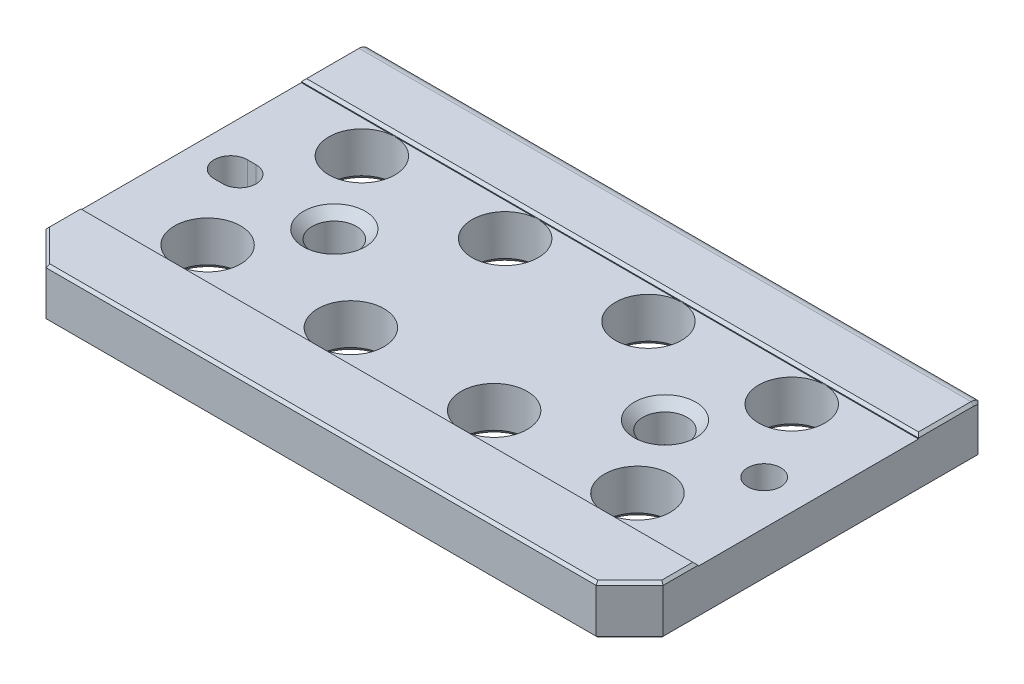
SolidWorks part; units mm, degrees
material "17-4 PH SSTL, H 1150"
ref_plane "Front" through (0, 0, 0) normal (0, 0, 1) x (1, 0, 0)
ref_plane "Top" through (0, 0, 0) normal (0, 1, 0) x (1, 0, 0)
ref_plane "Right" through (0, 0, 0) normal (1, 0, 0) x (0, 0, -1)
sketch "Sketch1" plane through (0, 0, 0) normal (1, 0, 0) x (0, 0, -1)
  line L0 (-47.625, 0) -> (-51.435, 0)
  line L1 (-47.625, -18.5166) -> (47.625, -18.5166)
  line L2 (-47.625, -18.5166) -> (-47.625, 0) construction
  line L3 (-47.625, 0) -> (47.625, 0)
  line L4 (47.625, -18.5166) -> (47.625, 0)
  line L5 (-51.435, 0) -> (-51.435, -18.5166)
  line L6 (-51.435, -18.5166) -> (-47.625, -18.5166)
  dimension "D1" = 18.5166
  dimension "D2" = 95.25
  dimension "D3" = 3.81
extrude "Extrude1" add sketch "Sketch1" along normal mid plane 177.8
sketch "Sketch10" plane through (0, 0, 0) normal (1, 0, 0) x (0, 0, -1)
  line L0 (47.625, 0) -> (47.625, -18.5166)
  line L2 (47.625, -18.5166) -> (49.657, -18.5166)
  line L3 (49.657, -18.5166) -> (49.657, -0.7354)
  line L6 (47.625, -18.5166) -> (47.625, 0) construction
  line L8 (47.625, 0) -> (-51.435, 0) construction
  line L9 (-51.435, -18.5166) -> (47.625, -18.5166) construction
  arc A1 (49.657, -0.7354) -> (47.625, 0) centre (47.625, -3.175) ccw
  dimension "D1" = 3.175
  dimension "D2" = 2.032
extrude "Extrude5" add sketch "Sketch10" against normal up to surface and the other way up to surface up to face at (-88.9, -9.2583, 1.905) other way up to face at (88.9, -9.2583, 1.905)
hole_wizard "3/4 (0.75) Diameter Hole1" positions "Sketch5" profile "Sketch4" hole size "3/4" standard "Ansi Inch" end condition up to next
sketch "Sketch5" plane through (100.5831, 0, 72.5126) normal (0, 1, 0) x (-1, 0, 0)
  line L0 (38.6706, -94.7376) -> (79.9456, -94.7376) construction
  line L1 (79.9456, -94.7376) -> (121.2206, -94.7376) construction
  line L2 (121.2206, -94.7376) -> (162.4956, -94.7376) construction
  point P0 (162.4956, -94.7376)
  point P1 (121.2206, -94.7376)
  point P3 (79.9456, -94.7376)
  point P5 (38.6706, -94.7376)
  point P7 (79.9456, -50.2876)
  point P9 (121.2206, -50.2876)
  point P11 (162.4956, -50.2876)
  point P24 (100.5831, -94.7376)
  point P38 (38.6706, -50.2876)
  dimension "D1" = 41.275
  dimension "D2" = 22.225
  dimension "D3" = 44.45
sketch "Sketch4" plane through (-61.9125, 0, -22.225) normal (1, 0, 0) x (0, 0, 1)
  line L0 (0, 0) -> (0, 18.5166)
  line L1 (0, 18.5166) -> (9.525, 18.5166)
  line L2 (9.525, 18.5166) -> (9.525, 0)
  line L5 (9.525, 0) -> (0, 0)
  line L11 (0, -6.35) -> (0, 107.95) construction
  dimension "Thru Hole Dia." = 19.05
  dimension "Thru Hole Depth" = 18.5166
sketch "Sketch6" plane through (0, 0, 0) normal (0, 1, 0) x (1, 0, 0)
  line L0 (-88.9, 47.625) -> (-88.9, -51.435) construction
  line L1 (-88.9, 31.75) -> (88.9, 31.75)
  line L5 (88.9, 47.625) -> (88.9, -51.435) construction
  line L8 (-88.9, 31.75) -> (-88.9, -31.75)
  line L9 (-88.9, -31.75) -> (88.9, -31.75)
  line L10 (88.9, -31.75) -> (88.9, 31.75)
  dimension "D1" = 31.75
  dimension "D2" = 31.75
extrude "Extrude2" cut sketch "Sketch6" against normal blind 1.016
chamfer "Chamfer10" distance 9.652 angle 45 2 edges at (88.9, -9.2583, 51.435) (-88.9, -9.2583, 51.435)
sketch "Sketch35" plane through (0, 0, 0) normal (1, 0, 0) x (0, 0, -1)
  line L0 (-51.435, -18.5166) -> (-51.435, 0) construction
  line L1 (-51.435, -14.224) -> (49.657, -14.224)
  line L2 (-51.435, -14.224) -> (-51.435, -18.5166)
  line L3 (-51.435, -18.5166) -> (49.657, -18.5166)
  line L4 (49.657, -14.224) -> (49.657, -18.5166)
  line L5 (47.625, 0) -> (47.625, -14.224) construction
  dimension "D1" = 14.224
extrude "Extrude11" cut sketch "Sketch35" against normal through all and the other way through all
hole_wizard "3/8 (0.375) Diameter Hole1" positions "Sketch18" profile "Sketch17" hole size "3/8" standard "Ansi Inch" end condition through all
sketch "Sketch18" plane through (11.6301, -14.224, 20.6862) normal (0, -1, 0) x (1, 0, 0)
  line L9 (-100.5301, -70.3432) -> (77.2699, -70.3432) construction
  line L10 (-11.6301, -70.3432) -> (-11.6301, -20.6862) construction
  point P0 (64.5699, -20.6862)
  dimension "D1" = 49.657
  dimension "D2" = 152.4
sketch "Sketch17" plane through (76.2, -14.224, 0) normal (1, 0, 0) x (0, 0, -1)
  line L0 (0, 0) -> (0, 14.224)
  line L1 (0, 14.224) -> (4.7714, 14.224)
  line L2 (4.7714, 14.224) -> (4.7714, 2.3406)
  line L3 (4.7714, 2.3406) -> (7.112, 0)
  line L5 (7.112, 0) -> (0, 0)
  line L6 (-4.7714, 2.3406) -> (-7.112, 0) construction
  line L11 (0, -6.35) -> (0, 107.95) construction
  dimension "Thru Hole Dia." = 9.5428
  dimension "Thru Hole Depth" = 14.224
  dimension "Near C'Sink Dia." = 14.224
  dimension "Near C'Sink Angle" = 90
sketch "Sketch19" plane through (0, -14.224, 0) normal (0, -1, 0) x (1, 0, 0)
  line L0 (-77.47, 0) -> (-74.93, 0) construction
  line L1 (-77.47, 4.7714) -> (-74.93, 4.7714)
  line L2 (-77.47, -4.7714) -> (-74.93, -4.7714)
  line L3 (-76.2, 0) -> (76.2, 0) construction
  arc A0 (-77.47, 4.7714) -> (-77.47, -4.7714) centre (-77.47, 0) ccw
  arc A1 (-74.93, -4.7714) -> (-74.93, 4.7714) centre (-74.93, 0) ccw
  circle A3 centre (76.2, 0) radius 4.7714 construction
  point P2 (-76.2, 0)
  dimension "D1" = 152.4
  dimension "D2" = 2.54
extrude "Extrude8" cut sketch "Sketch19" against normal through all
chamfer "Chamfer13" distance 2.286 angle 45 4 edges at (-76.2, -14.224, 4.7714) (-82.2414, -14.224, 0) (-70.1586, -14.224, 0) (-76.2, -14.224, -4.7714)
hole_wizard "1/2 (0.5) Diameter Hole4" positions "Sketch27" profile "Sketch26" hole size "1/2" standard "Ansi Inch" end condition through all
sketch "Sketch27" plane through (18.5069, -1.016, -8.2591) normal (0, 1, 0) x (-1, 0, 0)
  line L10 (-29.1181, 8.2591) -> (66.1319, 8.2591) construction
  line L15 (-43.4056, -13.9659) -> (-2.1306, -13.9659) construction
  line L16 (18.5069, 18.4353) -> (18.5069, -1.917) construction
  point P0 (66.1319, 8.2591)
  point P25 (-29.1181, 8.2591)
  point P44 (18.5069, 8.2591)
  dimension "D1" = 95.25
  dimension "D3" = 22.225
sketch "Sketch26" plane through (-47.625, -1.016, 0) normal (1, 0, 0) x (0, 0, 1)
  line L0 (0, 0) -> (0, 13.208)
  line L1 (0, 13.208) -> (8.89, 13.208)
  line L2 (6.3754, 10.6934) -> (6.3754, 2.5146)
  line L3 (6.3754, 2.5146) -> (8.89, 0)
  line L5 (8.89, 0) -> (0, 0)
  line L6 (-6.3754, 2.5146) -> (-8.89, 0) construction
  line L7 (8.89, 13.208) -> (6.3754, 10.6934)
  line L8 (-8.89, 13.208) -> (-6.3754, 10.6934) construction
  line L11 (0, -6.35) -> (0, 107.95) construction
  dimension "Thru Hole Dia." = 12.7508
  dimension "Thru Hole Depth" = 13.208
  dimension "Near C'Sink Dia." = 17.78
  dimension "Near C'Sink Angle" = 90
  dimension "Far C'Sink Dia." = 17.78
  dimension "Far C'Sink Angle" = 90
sketch "Sketch28" [suppressed] plane through (0, 0, 0) normal (1, 0, 0) x (0, 0, -1)
  line L0 (-51.435, -9.9401) -> (-51.435, -18.5166)
  line L1 (-51.435, -18.5166) -> (-51.435, 0) construction
  line L2 (-51.435, -18.5166) -> (49.657, -18.5166)
  line L3 (49.657, -18.5166) -> (49.657, -11.7224)
  line L4 (49.657, -18.5166) -> (49.657, -0.7354) construction
  line L5 (49.657, -11.7224) -> (-51.435, -9.9401)
  line L6 (47.625, 0) -> (47.625, -11.6865) construction
  dimension "D1" = 1.01
  dimension "D2" = 11.6865
extrude "Extrude9" [suppressed] cut sketch "Sketch28" against normal through all and the other way through all
hole_wizard "3/8 (0.375) Diameter Hole2" positions "Sketch30" profile "Sketch29" hole size "3/8" standard "Ansi Inch"
sketch "Sketch30" plane through (0, -10.8436, 0.1912) normal (0, -0.9998, 0.0176) x (1, 0, 0)
  line L1 (76.2, 0.2956) -> (-76.2, 0.2956) construction
  line L4 (0, -7.8232) -> (0, 7.8232) construction
  line L5 (-20.6375, -22.2215) -> (-61.9125, -22.2215) construction
  point P0 (76.2, 0.2956)
  point P10 (0, 0.2956)
  dimension "D1" = 22.5171
  dimension "D2" = 152.4
sketch "Sketch29" plane through (76.2, -10.8383, 0.4867) normal (1, 0, 0) x (0, -0.0176, -0.9998)
  line L0 (0, 0) -> (0, 11.7205)
  line L1 (0, 11.7205) -> (4.7714, 11.7205)
  line L2 (4.7714, 11.7205) -> (4.7714, 2.3406)
  line L3 (4.7714, 2.3406) -> (7.112, 0)
  line L5 (7.112, 0) -> (0, 0)
  line L6 (-4.7714, 2.3406) -> (-7.112, 0) construction
  line L11 (0, -6.35) -> (0, 107.95) construction
  dimension "Thru Hole Dia." = 9.5428
  dimension "Thru Hole Depth" = 11.7205
  dimension "Near C'Sink Dia." = 14.224
  dimension "Near C'Sink Angle" = 90
sketch "Sketch31" [suppressed] plane through (0, -10.8436, 0.1912) normal (0, -0.9998, 0.0176) x (1, 0, 0)
  line L0 (-77.47, 0.2956) -> (-74.93, 0.2956) construction
  line L1 (-77.47, 5.0669) -> (-74.93, 5.0669)
  line L2 (-77.47, -4.4758) -> (-74.93, -4.4758)
  arc A0 (-77.47, 5.0669) -> (-77.47, -4.4758) centre (-77.47, 0.2956) ccw
  arc A1 (-74.93, -4.4758) -> (-74.93, 5.0669) centre (-74.93, 0.2956) ccw
  circle A2 centre (76.2, 0.2956) radius 4.7714 construction
  point P2 (-76.2, 0.2956)
  dimension "D1" = 2.54
extrude "Extrude10" [suppressed] cut sketch "Sketch31" against normal through all
chamfer "Chamfer14" [suppressed] distance 2.286 angle 45
hole_wizard "1/2 (0.5) Diameter Hole5" positions "Sketch34" profile "Sketch33" hole size "1/2" standard "Ansi Inch"
sketch "Sketch34" plane through (0, -1.016, 0) normal (0, 1, 0) x (-1, 0, 0)
  line L0 (47.625, 0) -> (-47.625, 0) construction
  line L3 (0, 7.8232) -> (0, -7.8232) construction
  line L4 (-61.9125, -22.225) -> (-20.6375, -22.225) construction
  point P0 (47.625, 0)
  point P1 (-47.625, 0)
  point P9 (0, 0)
  dimension "D1" = 95.25
  dimension "D2" = 22.225
sketch "Sketch33" plane through (-47.625, -1.016, 0) normal (1, 0, 0) x (0, 0, 1)
  line L0 (0, 0) -> (0, 10.7064)
  line L1 (0, 10.7064) -> (8.89, 10.7064)
  line L2 (6.3754, 8.1918) -> (6.3754, 2.5146)
  line L3 (6.3754, 2.5146) -> (8.89, 0)
  line L5 (8.89, 0) -> (0, 0)
  line L6 (-6.3754, 2.5146) -> (-8.89, 0) construction
  line L7 (8.89, 10.7064) -> (6.3754, 8.1918)
  line L8 (-8.89, 10.7064) -> (-6.3754, 8.1918) construction
  line L11 (0, -6.35) -> (0, 107.95) construction
  dimension "Thru Hole Dia." = 12.7
  dimension "Thru Hole Depth" = 10.7064
  dimension "Near C'Sink Dia." = 13.97
  dimension "Near C'Sink Angle" = 90
  dimension "Far C'Sink Dia." = 19.05
  dimension "Far C'Sink Angle" = 90
sketch "Sketch36" [suppressed] plane through (0, 0, 0) normal (1, 0, 0) x (0, 0, -1)
  line L0 (-51.435, -18.5155) -> (-51.435, -18.5166)
  line L1 (-51.435, -18.5166) -> (-51.435, 0) construction
  line L2 (-51.435, -18.5166) -> (49.657, -18.5166)
  line L3 (49.657, -18.5166) -> (49.657, -16.7333)
  line L4 (49.657, -18.5166) -> (49.657, -0.7354) construction
  line L5 (49.657, -16.7333) -> (-51.435, -18.5155)
  line L6 (47.625, 0) -> (47.625, -16.7691) construction
  dimension "D1" = 1.01
  dimension "D2" = 16.7691
extrude "Extrude12" [suppressed] cut sketch "Sketch36" against normal through all and the other way through all
hole_wizard "3/8 (0.375) Diameter Hole3" positions "Sketch38" profile "Sketch37" hole size "3/8" standard "Ansi Inch"
sketch "Sketch38" plane through (0, -17.6032, -0.3103) normal (0, -0.9998, -0.0176) x (1, 0, 0)
  line L0 (76.2, -0.2531) -> (-76.2, -0.2531) construction
  line L3 (0, -10.1841) -> (0, 10.1841) construction
  line L4 (-20.6375, -22.2215) -> (-61.9125, -22.2215) construction
  point P0 (76.2, -0.2531)
  point P7 (0, -0.2531)
  dimension "D1" = 152.4
  dimension "D2" = 21.9685
sketch "Sketch37" plane through (76.2, -17.5988, -0.5634) normal (1, 0, 0) x (0, 0.0176, -0.9998)
  line L0 (0, 0) -> (0, 18.5126)
  line L1 (0, 18.5126) -> (4.7714, 18.5126)
  line L2 (4.7714, 18.5126) -> (4.7714, 2.3406)
  line L3 (4.7714, 2.3406) -> (7.112, 0)
  line L5 (7.112, 0) -> (0, 0)
  line L6 (-4.7714, 2.3406) -> (-7.112, 0) construction
  line L11 (0, -6.35) -> (0, 107.95) construction
  dimension "Thru Hole Dia." = 9.5428
  dimension "Thru Hole Depth" = 18.5126
  dimension "Near C'Sink Dia." = 14.224
  dimension "Near C'Sink Angle" = 90
sketch "Sketch39" [suppressed] plane through (0, -17.6032, -0.3103) normal (0, -0.9998, -0.0176) x (1, 0, 0)
  line L0 (-77.47, -0.2531) -> (-74.93, -0.2531) construction
  line L1 (-77.47, 4.5183) -> (-74.93, 4.5183)
  line L2 (-77.47, -5.0245) -> (-74.93, -5.0245)
  arc A0 (-77.47, 4.5183) -> (-77.47, -5.0245) centre (-77.47, -0.2531) ccw
  arc A1 (-74.93, -5.0245) -> (-74.93, 4.5183) centre (-74.93, -0.2531) ccw
  circle A2 centre (76.2, -0.2531) radius 4.7714 construction
  point P2 (-76.2, -0.2531)
  dimension "D1" = 2.54
extrude "Extrude13" [suppressed] cut sketch "Sketch39" against normal through all
chamfer "Chamfer15" [suppressed] distance 2.286 angle 45
hole_wizard "1/2 (0.5) Diameter Hole6" positions "Sketch41" profile "Sketch40" hole size "1/2" standard "Ansi Inch"
sketch "Sketch41" plane through (0, -1.016, 0) normal (0, 1, 0) x (-1, 0, 0)
  line L0 (-47.625, 0) -> (47.625, 0) construction
  line L3 (0, 10.1841) -> (0, -10.1841) construction
  line L4 (-61.9125, -22.225) -> (-20.6375, -22.225) construction
  point P0 (47.625, 0)
  point P1 (-47.625, 0)
  point P9 (0, 0)
  dimension "D1" = 95.25
  dimension "D2" = 22.225
sketch "Sketch40" plane through (-47.625, -1.016, 0) normal (1, 0, 0) x (0, 0, 1)
  line L0 (0, 0) -> (0, 17.4995)
  line L1 (0, 17.4995) -> (8.89, 17.4995)
  line L2 (6.3754, 14.9849) -> (6.3754, 2.5146)
  line L3 (6.3754, 2.5146) -> (8.89, 0)
  line L5 (8.89, 0) -> (0, 0)
  line L6 (-6.3754, 2.5146) -> (-8.89, 0) construction
  line L7 (8.89, 17.4995) -> (6.3754, 14.9849)
  line L8 (-8.89, 17.4995) -> (-6.3754, 14.9849) construction
  line L11 (0, -6.35) -> (0, 107.95) construction
  dimension "Thru Hole Dia." = 12.7508
  dimension "Thru Hole Depth" = 17.4995
  dimension "Near C'Sink Dia." = 17.78
  dimension "Near C'Sink Angle" = 90
  dimension "Far C'Sink Dia." = 17.78
  dimension "Far C'Sink Angle" = 90
chamfer "Chamfer16" distance 0.762 angle 45 19 edges at (-88.9, -14.224, -3.937) (-84.074, -14.224, 46.609) (0, -14.224, 51.435) (84.074, -14.224, 46.609) (88.9, -14.224, -3.937) (0, -14.224, -49.657) (-88.9, -0.1895, -48.7055) (88.9, -0.1895, -48.7055) (88.9, 0, -39.6875) (-88.9, 0, -39.6875) (-88.9, 0, 36.7665) (-84.074, 0, 46.609) (88.9, 0, 36.7665) (84.074, 0, 46.609) (0, 0, 51.435) (-88.9, -7.4797, -49.657) (88.9, -7.4797, -49.657) (0, 0, -31.75) (0, 0, 31.75)
chamfer "Chamfer19" distance 1.524 angle 45 8 edges at (-61.9125, -14.224, 31.75) (-20.6375, -14.224, 31.75) (20.6375, -14.224, 31.75) (61.9125, -14.224, 31.75) (-61.9125, -14.224, -12.7) (-20.6375, -14.224, -12.7) (20.6375, -14.224, -12.7) (61.9125, -14.224, -12.7)
chamfer "Chamfer17" [suppressed] distance 0.762 angle 45
chamfer "Chamfer20" [suppressed] distance 1.524 angle 45
chamfer "Chamfer18" [suppressed] distance 0.762 angle 45
chamfer "Chamfer21" [suppressed] distance 1.524 angle 45
